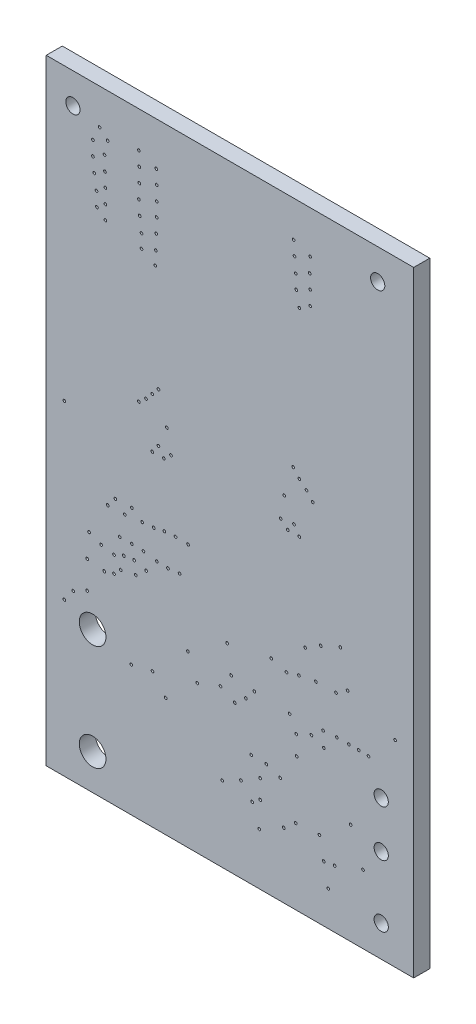
SolidWorks part; units mm, degrees
ref_plane "Front Plane" through (0, 0, 0) normal (0, 0, 1) x (1, 0, 0)
ref_plane "Top Plane" through (0, 0, 0) normal (0, 1, 0) x (1, 0, 0)
ref_plane "Right Plane" through (0, 0, 0) normal (1, 0, 0) x (0, 0, -1)
ref_plane "Dielectric_Layer Layer 1" through (0, 0, 0.9144) normal (0, 0, 1) x (1, 0, 0)
sketch "Sketch1" plane through (0, 0, 0) normal (0, 0, 1) x (1, 0, 0)
  line L0 (0, 0) -> (0, 35.052)
  line L1 (0, 35.052) -> (20.931, 35.052)
  line L2 (20.931, 35.052) -> (20.931, 0)
  line L3 (20.931, 0) -> (0, 0)
extrude "Board_Outline" add sketch "Sketch1" along normal blind 0.9144 separate body
sketch "Sketch2" plane through (0, 0, 0) normal (0, 0, 1) x (1, 0, 0)
  circle A0 centre (14.2414, 8.6868) radius 0.0762
  circle A1 centre (6.0499, 7.6962) radius 0.0762
  circle A2 centre (9.9234, 8.89) radius 0.0762
  circle A3 centre (4.8434, 7.4168) radius 0.0762
  circle A4 centre (10.533, 9.7282) radius 0.0762
  circle A5 centre (19.87, 11.21) radius 0.0762
  circle A6 centre (6.8678, 20.1168) radius 0.0762
  circle A7 centre (13.5556, 20.1168) radius 0.0762
  circle A8 centre (11.0918, 4.826) radius 0.0762
  circle A9 centre (1.5414, 9.398) radius 0.0762
  circle A10 centre (11.3712, 9.017) radius 0.0762
  circle A11 centre (13.8604, 9.4996) radius 0.0762
  circle A12 centre (14.21, 4.28) radius 0.0762
  circle A13 centre (18.04, 3.9) radius 0.0762
  circle A14 centre (17.7974, 9.6774) radius 0.0762
  circle A15 centre (8.6026, 8.382) radius 0.0762
  circle A16 centre (17.2386, 9.6774) radius 0.0762
  circle A17 centre (10.025, 4.2926) radius 0.0762
  circle A18 centre (12.184, 4.4196) radius 0.0762
  circle A19 centre (12.184, 5.4864) radius 0.0762
  circle A20 centre (16.5528, 9.6774) radius 0.0762
  circle A21 centre (15.7654, 9.6266) radius 0.0762
  circle A22 centre (13.327, 6.0706) radius 0.0762
  circle A23 centre (11.7268, 4.0894) radius 0.0762
  circle A24 centre (2.3311, 11.3792) radius 0.0762
  circle A25 centre (3.04, 33.02) radius 0.0762
  circle A26 centre (3.302, 11.2522) radius 0.0762
  circle A27 centre (3.4972, 32.5882) radius 0.0762
  circle A28 centre (3.8608, 11.4046) radius 0.0762
  circle A29 centre (2.659, 32.2072) radius 0.0762
  circle A30 centre (4.2418, 11.7856) radius 0.0762
  circle A31 centre (3.3194, 31.8008) radius 0.0762
  circle A32 centre (5.1054, 11.9634) radius 0.0762
  circle A33 centre (2.659, 31.3944) radius 0.0762
  circle A34 centre (2.4384, 12.7508) radius 0.0762
  circle A35 centre (3.3448, 30.988) radius 0.0762
  circle A36 centre (3.1242, 12.4714) radius 0.0762
  circle A37 centre (2.7352, 30.607) radius 0.0762
  circle A38 centre (3.8608, 12.3444) radius 0.0762
  circle A39 centre (3.3702, 30.2006) radius 0.0762
  circle A40 centre (4.4196, 12.573) radius 0.0762
  circle A41 centre (2.8622, 29.7942) radius 0.0762
  circle A42 centre (5.0038, 12.6492) radius 0.0762
  circle A43 centre (3.3702, 29.3878) radius 0.0762
  circle A44 centre (5.6896, 12.4714) radius 0.0762
  circle A45 centre (2.8876, 29.0068) radius 0.0762
  circle A46 centre (4.191, 13.3858) radius 0.0762
  circle A47 centre (3.3702, 28.6004) radius 0.0762
  circle A48 centre (4.8768, 13.3858) radius 0.0762
  circle A49 centre (5.2752, 32.9946) radius 0.0762
  circle A50 centre (5.5372, 13.3604) radius 0.0762
  circle A51 centre (6.2658, 32.5882) radius 0.0762
  circle A52 centre (6.2992, 13.2334) radius 0.0762
  circle A53 centre (5.3006, 32.2072) radius 0.0762
  circle A54 centre (6.9342, 13.208) radius 0.0762
  circle A55 centre (6.2912, 31.8008) radius 0.0762
  circle A56 centre (7.5946, 13.2842) radius 0.0762
  circle A57 centre (5.3006, 31.3944) radius 0.0762
  circle A58 centre (3.5052, 14.605) radius 0.0762
  circle A59 centre (6.2912, 30.988) radius 0.0762
  circle A60 centre (3.937, 15.1384) radius 0.0762
  circle A61 centre (5.2752, 30.5816) radius 0.0762
  circle A62 centre (4.4704, 14.6304) radius 0.0762
  circle A63 centre (6.2912, 30.2006) radius 0.0762
  circle A64 centre (4.8768, 15.1638) radius 0.0762
  circle A65 centre (5.326, 29.7942) radius 0.0762
  circle A66 centre (5.461, 14.7574) radius 0.0762
  circle A67 centre (6.2658, 29.3878) radius 0.0762
  circle A68 centre (6.1214, 14.8082) radius 0.0762
  circle A69 centre (5.4276, 28.9814) radius 0.0762
  circle A70 centre (6.731, 14.9352) radius 0.0762
  circle A71 centre (6.2404, 28.5496) radius 0.0762
  circle A72 centre (7.366, 14.986) radius 0.0762
  circle A73 centre (5.4276, 28.2194) radius 0.0762
  circle A74 centre (8.0772, 14.9606) radius 0.0762
  circle A75 centre (6.215, 27.7876) radius 0.0762
  circle A76 centre (6.0372, 18.5166) radius 0.0762
  circle A77 centre (5.2752, 20.5994) radius 0.0762
  circle A78 centre (6.3928, 18.9738) radius 0.0762
  circle A79 centre (5.6816, 20.955) radius 0.0762
  circle A80 centre (6.6976, 18.5166) radius 0.0762
  circle A81 centre (6.0372, 21.3614) radius 0.0762
  circle A82 centre (7.104, 18.8722) radius 0.0762
  circle A83 centre (6.3928, 21.7678) radius 0.0762
  circle A84 centre (14.089, 32.9946) radius 0.0762
  circle A85 centre (12.819, 11.7094) radius 0.0762
  circle A86 centre (15.0288, 32.639) radius 0.0762
  circle A87 centre (13.6826, 11.4554) radius 0.0762
  circle A88 centre (14.1398, 32.2072) radius 0.0762
  circle A89 centre (14.3938, 11.6586) radius 0.0762
  circle A90 centre (15.0034, 31.8008) radius 0.0762
  circle A91 centre (15.359, 11.8364) radius 0.0762
  circle A92 centre (14.216, 31.3944) radius 0.0762
  circle A93 centre (16.502, 11.8618) radius 0.0762
  circle A94 centre (15.0288, 31.0134) radius 0.0762
  circle A95 centre (17.1624, 12.2936) radius 0.0762
  circle A96 centre (14.2414, 30.607) radius 0.0762
  circle A97 centre (14.7494, 13.208) radius 0.0762
  circle A98 centre (15.0288, 30.2006) radius 0.0762
  circle A99 centre (15.6384, 13.7414) radius 0.0762
  circle A100 centre (14.4192, 29.7942) radius 0.0762
  circle A101 centre (16.756, 14.224) radius 0.0762
  circle A102 centre (14.4192, 18.5166) radius 0.0762
  circle A103 centre (15.1812, 20.5994) radius 0.0762
  circle A104 centre (14.1144, 18.9738) radius 0.0762
  circle A105 centre (14.8256, 21.0058) radius 0.0762
  circle A106 centre (13.7588, 18.5166) radius 0.0762
  circle A107 centre (14.4192, 21.3614) radius 0.0762
  circle A108 centre (13.3524, 18.8722) radius 0.0762
  circle A109 centre (14.0636, 21.7678) radius 0.0762
  circle A110 centre (16.0702, 1.9812) radius 0.0762
  circle A111 centre (12.5396, 6.35) radius 0.0762
  circle A112 centre (15.8094, 3.195) radius 0.0762
  circle A113 centre (10.7362, 8.4836) radius 0.0762
  circle A114 centre (17.3402, 5.7658) radius 0.0762
  circle A115 centre (15.5622, 4.3688) radius 0.0762
  circle A116 centre (16.4296, 3.2888) radius 0.0762
  circle A117 centre (11.676, 6.3754) radius 0.0762
  circle A118 centre (1.0334, 18.5166) radius 0.0762
  circle A119 centre (1.0334, 8.7122) radius 0.0762
  circle A120 centre (10.3044, 11.2014) radius 0.0762
  circle A121 centre (15.8162, 8.7884) radius 0.0762
  circle A122 centre (13.5302, 3.7084) radius 0.0762
  circle A123 centre (15.105, 9.0678) radius 0.0762
  circle A124 centre (12.1332, 2.9464) radius 0.0762
  circle A125 centre (14.2636, 7.6016) radius 0.0762
  circle A126 centre (2.3288, 9.8044) radius 0.0762
  circle A127 centre (8.0692, 9.6774) radius 0.0762
  circle A128 centre (11.8538, 9.6012) radius 0.0762
  circle A129 centre (18.3562, 9.652) radius 0.0762
  circle A130 centre (6.7992, 6.7564) radius 0.0762
extrude "NPTH" cut sketch "Sketch2" along normal through all
sketch "Sketch3" plane through (0, 0, 0) normal (0, 0, 1) x (1, 0, 0)
  circle A0 centre (19.08, 5.31) radius 0.405
  circle A1 centre (18.88, 33.32) radius 0.405
  circle A2 centre (2.64, 8.05) radius 0.76
  circle A3 centre (2.64, 2.03) radius 0.76
  circle A4 centre (19.08, 7.96) radius 0.405
  circle A5 centre (1.52, 33.32) radius 0.405
  circle A6 centre (19.08, 1.78) radius 0.405
extrude "PTH" cut sketch "Sketch3" along normal through all
